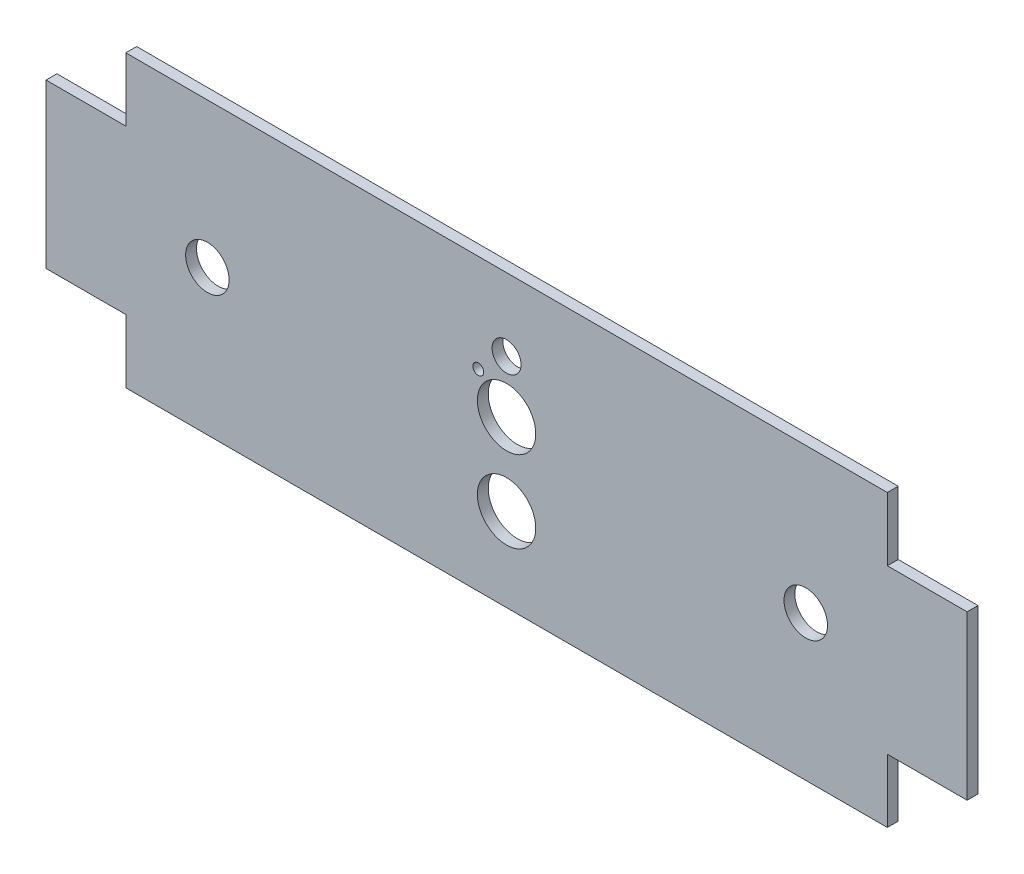
SolidWorks part; units mm, degrees
ref_plane "Alzado" through (0, 0, 0) normal (0, 0, 1) x (1, 0, 0)
ref_plane "Planta" through (0, 0, 0) normal (0, 1, 0) x (1, 0, 0)
ref_plane "Vista lateral" through (0, 0, 0) normal (1, 0, 0) x (0, 0, -1)
sketch "Croquis1" plane through (0, 0, 0) normal (0, 0, 1) x (1, 0, 0)
  line L0 (0, 0) -> (-116, 0) construction
  line L1 (105, -30) -> (-105, -30)
  line L2 (105, -30) -> (105, 30)
  line L3 (105, 30) -> (-105, 30)
  line L4 (-105, -30) -> (-105, 30)
  line L5 (105, -30) -> (-105, 30) construction
  line L6 (105, 30) -> (-105, -30) construction
  line L7 (0, 0) -> (116, 0) construction
  line L8 (-127, -22.5) -> (-105, -22.5)
  line L9 (-127, -22.5) -> (-127, 22.5)
  line L10 (-127, 22.5) -> (-105, 22.5)
  line L11 (-105, -22.5) -> (-105, 22.5)
  line L12 (-127, -22.5) -> (-105, 22.5) construction
  line L13 (-127, 22.5) -> (-105, -22.5) construction
  line L15 (127, 22.5) -> (105, 22.5)
  line L16 (127, 22.5) -> (127, -22.5)
  line L17 (127, -22.5) -> (105, -22.5)
  line L18 (105, 22.5) -> (105, -22.5)
  line L19 (127, 22.5) -> (105, -22.5) construction
  line L20 (127, -22.5) -> (105, 22.5) construction
  point P0 (0, 0)
  dimension "D1" = 210
  dimension "D2" = 60
  dimension "D3" = 45
  dimension "D4" = 22
  dimension "D5" = 22
  dimension "D6" = 45
extrude "Saliente-Extruir1" add sketch "Croquis1" along normal blind 3 contours L10 L9 L8 L4 | L4 L1 L2 L3 | L16 L17 L18 L15
sketch "Croquis2" plane through (0, 0, 3) normal (0, 0, 1) x (1, 0, 0)
  line L0 (0, 0) -> (-82.5, 0) construction
  line L3 (82.5, 0) -> (0, 0) construction
  circle A0 centre (82.5, 0) radius 6
  circle A1 centre (-82.5, 0) radius 6
  dimension "D2" = 12
  dimension "D1" = 165
extrude "Cortar-Extruir1" cut sketch "Croquis2" against normal up to next
sketch "Croquis3" plane through (0, 0, 3) normal (0, 0, 1) x (1, 0, 0)
  line L0 (0, 0) -> (0, 20) construction
  circle A0 centre (0, 20) radius 4
  dimension "D1" = 8
  dimension "D2" = 20
extrude "Cortar-Extruir2" cut sketch "Croquis3" against normal up to next
sketch "Croquis4" plane through (0, 0, 3) normal (0, 0, 1) x (1, 0, 0)
  line L0 (105, -30) -> (105, -22.5) construction
  line L1 (-105, -30) -> (105, -30)
  line L2 (-105, -30) -> (-105, -40)
  line L3 (-105, -40) -> (105, -40)
  line L4 (105, -30) -> (105, -40)
  dimension "D1" = 10
extrude "Saliente-Extruir2" add sketch "Croquis4" against normal up to surface (3 mm away) up to face at (4, 20, 0)
sketch "Croquis5" plane through (0, 0, 3) normal (0, 0, 1) x (1, 0, 0)
  line L0 (105, 22.5) -> (105, 30) construction
  line L1 (-105, 30) -> (105, 30)
  line L2 (-105, 30) -> (-105, 40)
  line L3 (-105, 40) -> (105, 40)
  line L4 (105, 30) -> (105, 40)
  dimension "D1" = 10
extrude "Saliente-Extruir3" add sketch "Croquis5" against normal up to surface (3 mm away) up to face at (4, 20, 0)
sketch "Croquis6" plane through (0, 0, 3) normal (0, 0, 1) x (1, 0, 0)
  line L0 (0, 20) -> (0, 5.5) construction
  line L1 (0, 5.5) -> (-7.8, 5.5) construction
  line L2 (-7.8, 5.5) -> (-7.8, 13.05) construction
  line L3 (0, 5.5) -> (0, -17) construction
  circle A0 centre (-7.8, 13.05) radius 1.5
  circle A1 centre (0, 5.5) radius 8.05
  circle A2 centre (0, -17) radius 8.05
  dimension "D1" = 3
  dimension "D4" = 16.1
  dimension "D2" = 7.8
  dimension "D3" = 7.55
  dimension "D5" = 14.5
  dimension "D6" = 22.5
extrude "Cortar-Extruir3" cut sketch "Croquis6" against normal up to next
